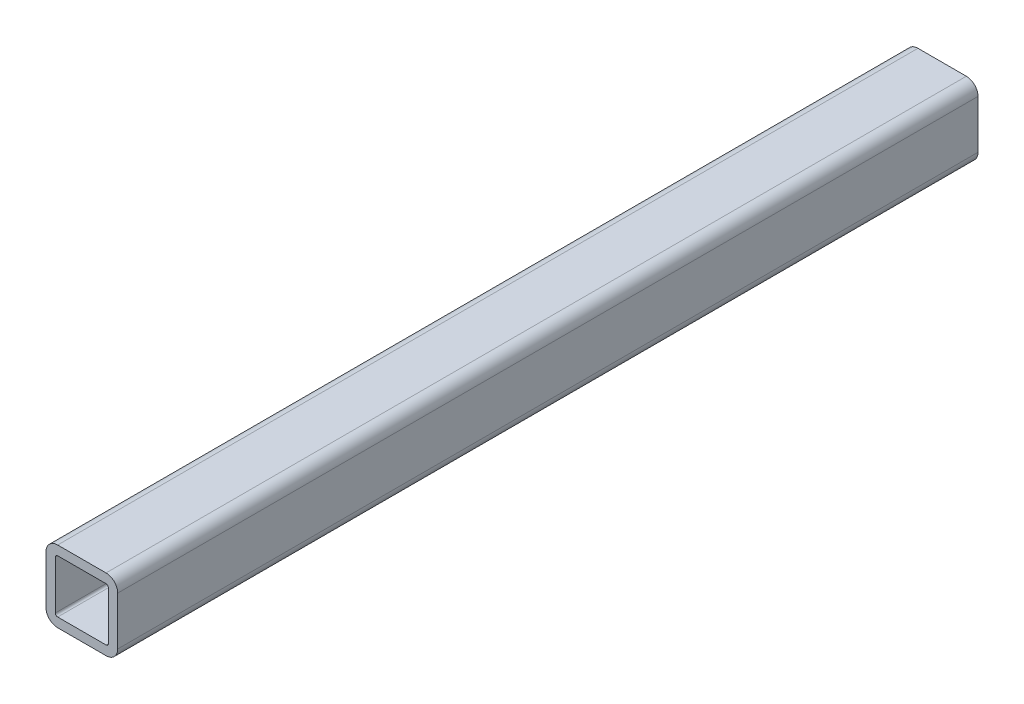
SolidWorks part; units mm, degrees
material "AISI 304"
ref_plane "Front" through (0, 0, 0) normal (0, 0, 1) x (1, 0, 0)
ref_plane "Top" through (0, 0, 0) normal (0, 1, 0) x (1, 0, 0)
ref_plane "Right" through (0, 0, 0) normal (1, 0, 0) x (0, 0, -1)
sketch "Sketch1" plane through (0, 0, 0) normal (0, 0, 1) x (1, 0, 0)
  line L0 (-4.699, 0) -> (-6.35, 0) construction
  line L1 (4.2863, -6.35) -> (-4.2863, -6.35)
  line L2 (6.35, -4.2863) -> (6.35, 4.2863)
  line L3 (4.2863, 6.35) -> (-4.2863, 6.35)
  line L4 (-6.35, -4.2863) -> (-6.35, 4.2863)
  line L5 (6.35, -6.35) -> (-6.35, 6.35) construction
  line L6 (6.35, 6.35) -> (-6.35, -6.35) construction
  line L7 (4.2863, 4.699) -> (-4.2863, 4.699)
  line L8 (4.699, 4.2863) -> (4.699, -4.2863)
  line L9 (4.2863, -4.699) -> (-4.2863, -4.699)
  line L10 (-4.699, 4.2863) -> (-4.699, -4.2863)
  line L11 (4.699, 4.699) -> (-4.699, -4.699) construction
  line L12 (4.699, -4.699) -> (-4.699, 4.699) construction
  line L13 (0, -4.699) -> (0, -6.35) construction
  arc A0 (-4.2863, -4.699) -> (-4.699, -4.2863) centre (-4.2863, -4.2863) cw
  arc A1 (4.699, -4.2863) -> (4.2863, -4.699) centre (4.2863, -4.2863) cw
  arc A2 (4.2863, 4.699) -> (4.699, 4.2863) centre (4.2863, 4.2863) cw
  arc A3 (-4.2863, 4.699) -> (-4.699, 4.2863) centre (-4.2863, 4.2863) ccw
  arc A4 (4.2863, -6.35) -> (6.35, -4.2863) centre (4.2863, -4.2863) ccw
  arc A5 (6.35, 4.2863) -> (4.2863, 6.35) centre (4.2863, 4.2863) ccw
  arc A6 (-4.2863, 6.35) -> (-6.35, 4.2863) centre (-4.2863, 4.2863) ccw
  arc A7 (-4.2863, -6.35) -> (-6.35, -4.2863) centre (-4.2863, -4.2863) cw
  point P0 (0, 0)
  point P6 (0, 0)
  dimension "D4" = 2.0638
  dimension "Outside Width" = 12.7
  dimension "Ouside Height" = 12.7
  dimension "D5" = 1.651
  dimension "Inside Width" = 9.398
  dimension "Wall Thickness" = 1.651
sketch "Sketch2" plane through (0, 0, 0) normal (1, 0, 0) x (0, 0, -1)
  line L0 (-76.2, 0) -> (76.2, 0) construction
  line L1 (76.2, -6.35) -> (76.2, 6.35)
  line L2 (-76.2, -6.35) -> (-76.2, 6.35)
  line L3 (0, -6.35) -> (0, 6.35) construction
  point P3 (-65.0875, 0)
  point P6 (76.2, 0)
  point P9 (-76.2, 0)
  point P12 (0, 0)
  point P13 (65.0875, 0)
  dimension "D1" = 11.1125
  dimension "Length" = 152.4
sketch "Sketch4" plane through (0, 0, 0) normal (0, 0, 1) x (1, 0, 0)
  line L0 (6.35, -4.2863) -> (6.35, 4.2863) construction
  line L1 (4.2863, 6.35) -> (-4.2863, 6.35) construction
  line L2 (-6.35, -4.2863) -> (-6.35, 4.2863) construction
  line L3 (4.2863, -6.35) -> (-4.2863, -6.35) construction
  line L4 (4.699, 4.2863) -> (4.699, -4.2863) construction
  line L5 (4.2863, -4.699) -> (-4.2863, -4.699) construction
  line L6 (-4.699, 4.2863) -> (-4.699, -4.2863) construction
  line L7 (4.2863, 4.699) -> (-4.2863, 4.699) construction
  line L8 (6.35, -4.2863) -> (6.35, 4.2863)
  line L9 (4.2863, 6.35) -> (-4.2863, 6.35)
  line L10 (-6.35, -4.2863) -> (-6.35, 4.2863)
  line L11 (4.2863, -6.35) -> (-4.2863, -6.35)
  line L12 (4.699, 4.2863) -> (4.699, -4.2863)
  line L13 (4.2863, -4.699) -> (-4.2863, -4.699)
  line L14 (-4.699, 4.2863) -> (-4.699, -4.2863)
  line L15 (4.2863, 4.699) -> (-4.2863, 4.699)
  arc A0 (6.35, 4.2863) -> (4.2863, 6.35) centre (4.2863, 4.2863) ccw construction
  arc A1 (-4.2863, 6.35) -> (-6.35, 4.2863) centre (-4.2863, 4.2863) ccw construction
  arc A2 (-6.35, -4.2863) -> (-4.2863, -6.35) centre (-4.2863, -4.2863) ccw construction
  arc A3 (4.2863, -6.35) -> (6.35, -4.2863) centre (4.2863, -4.2863) ccw construction
  arc A4 (4.2863, -4.699) -> (4.699, -4.2863) centre (4.2863, -4.2863) ccw construction
  arc A5 (-4.699, -4.2863) -> (-4.2863, -4.699) centre (-4.2863, -4.2863) ccw construction
  arc A6 (-4.2863, 4.699) -> (-4.699, 4.2863) centre (-4.2863, 4.2863) ccw construction
  arc A7 (4.699, 4.2863) -> (4.2863, 4.699) centre (4.2863, 4.2863) ccw construction
  arc A8 (6.35, 4.2863) -> (4.2863, 6.35) centre (4.2863, 4.2863) ccw
  arc A9 (-4.2863, 6.35) -> (-6.35, 4.2863) centre (-4.2863, 4.2863) ccw
  arc A10 (-6.35, -4.2863) -> (-4.2863, -6.35) centre (-4.2863, -4.2863) ccw
  arc A11 (4.2863, -6.35) -> (6.35, -4.2863) centre (4.2863, -4.2863) ccw
  arc A12 (4.2863, -4.699) -> (4.699, -4.2863) centre (4.2863, -4.2863) ccw
  arc A13 (-4.699, -4.2863) -> (-4.2863, -4.699) centre (-4.2863, -4.2863) ccw
  arc A14 (-4.2863, 4.699) -> (-4.699, 4.2863) centre (-4.2863, 4.2863) ccw
  arc A15 (4.699, 4.2863) -> (4.2863, 4.699) centre (4.2863, 4.2863) ccw
extrude "Boss-Extrude1" add sketch "Sketch4" along normal mid plane 152.4
equation "\"D1@Sketch2\"=\"Outside Width@Sketch1\"*.875"
equation "\"D1@Boss-Extrude1\"=\"Length@Sketch2\""
equation "\"D4@Sketch1\"=\"D5@Sketch1\"*1.25"
